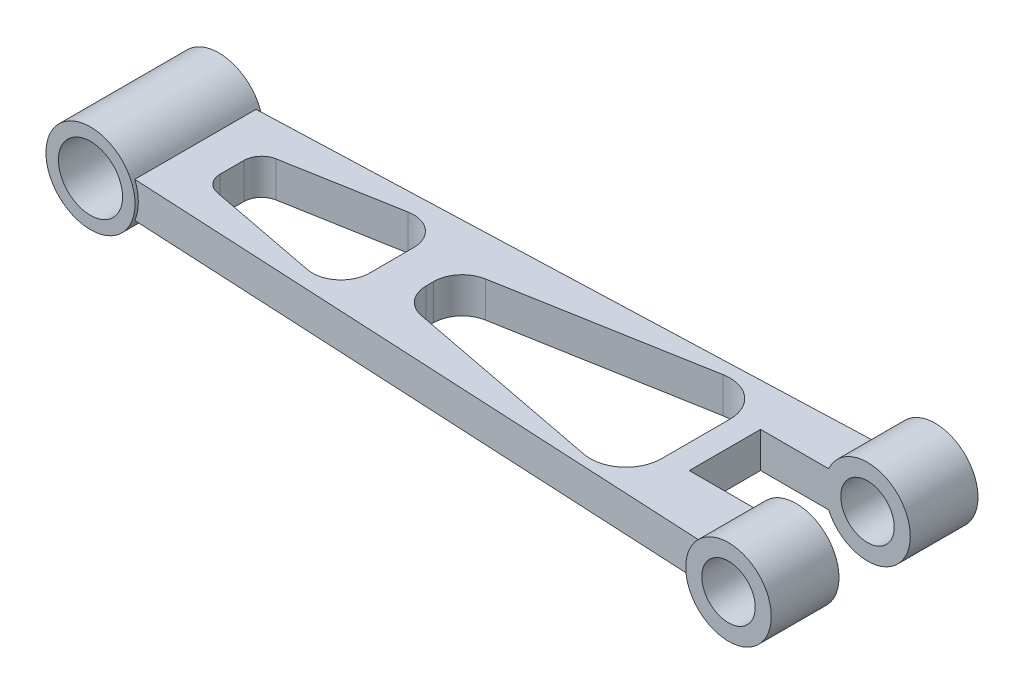
SolidWorks part; units mm, degrees
material "Ti-6Al-4VSolution treated and aged (SS)"
ref_plane "Front Plane" through (0, 0, 0) normal (0, 0, 1) x (1, 0, 0)
ref_plane "Top Plane" through (0, 0, 0) normal (0, 1, 0) x (1, 0, 0)
ref_plane "Right Plane" through (0, 0, 0) normal (1, 0, 0) x (0, 0, -1)
sketch "Sketch1" plane through (0, 0, 0) normal (0, 0, 1) x (1, 0, 0)
  line L0 (-142.6024, 0) -> (128.1696, 0) construction
  line L1 (0, 42.0831) -> (0, -47.0217) construction
  circle A1 centre (-95, 0) radius 9
  dimension "D1" = 18
  dimension "D3" = 95
extrude "Boss-Extrude2" add sketch "Sketch1" along normal mid plane 36
sketch "Sketch2" plane through (0, 0, 0) normal (0, 0, 1) x (1, 0, 0)
  line L0 (-174.7193, 0) -> (396.8583, 0) construction
  circle A1 centre (95, 0) radius 7.5
  dimension "D1" = 15
  dimension "D3" = 95
extrude "Boss-Extrude3" add sketch "Sketch2" along normal mid plane 58 separate body
sketch "Sketch5" plane through (0, 0, 0) normal (0, 1, 0) x (1, 0, 0)
  line L0 (-120.9467, 0) -> (118.8255, 0) construction
  line L1 (-86, -16.9) -> (-86, 16.8979)
  line L2 (-86, -18) -> (-86, 18) construction
  line L3 (-86, 16.8979) -> (87.5, 23.2428)
  line L5 (87.5, 23.2428) -> (87.5, -25.7343)
  line L6 (87.5, -25.7343) -> (-86, -16.9)
  line L7 (87.5, 29) -> (87.5, -29) construction
  point P7 (-55, 18.0315)
  point P12 (-55, -18.4785)
  dimension "D1" = 31
  dimension "D2" = 31
  dimension "D3" = 5.009
  dimension "D4" = 36.51
  dimension "D5" = 48.9771
  dimension "D6" = 23.2428
extrude "Boss-Extrude5" add sketch "Sketch5" along normal mid plane 10 separate body
sketch "Sketch7" plane through (0, 0, 0) normal (0, 0, 1) x (1, 0, 0)
  circle A0 centre (-95, 0) radius 12.5
  dimension "D1" = 25
extrude "Boss-Extrude6" add sketch "Sketch7" along normal mid plane 36
sketch "Sketch8" plane through (0, 0, 0) normal (0, 0, 1) x (1, 0, 0)
  circle A0 centre (95, 0) radius 12
  dimension "D1" = 24
extrude "Boss-Extrude7" add sketch "Sketch8" along normal mid plane 58
sketch "Sketch9" plane through (0, 0, 0) normal (0, 0, 1) x (1, 0, 0)
  circle A0 centre (-95, 0) radius 9
  circle A1 centre (95, 0) radius 7.5
  dimension "D1" = 18
  dimension "D2" = 15
extrude "Cut-Extrude1" cut sketch "Sketch9" against normal mid plane 58
sketch "Sketch10" plane through (0, 5, 0) normal (0, 1, 0) x (1, 0, 0)
  line L0 (-132.4159, 0) -> (132.5611, 0) construction
  line L1 (107, -29) -> (107, 29) construction
  line L2 (65, 10) -> (107, 10)
  line L3 (65, 10) -> (65, -10)
  line L4 (65, -10) -> (107, -10)
  line L5 (107, 10) -> (107, -10)
  dimension "D1" = 20
  dimension "D2" = 42
  dimension "D3" = 10
extrude "Cut-Extrude2" cut sketch "Sketch10" against normal mid plane 58
sketch "Sketch11" plane through (0, 5, 0) normal (0, 1, 0) x (1, 0, 0)
  line L0 (-145.9443, 0) -> (154.4776, 0) construction
  line L1 (-72.8284, 2.8417) -> (-72.8284, -3.7789)
  line L2 (-68.7751, -8.6885) -> (-37.3432, -14.7498)
  line L3 (-27.8284, -6.8945) -> (-27.8284, 5.4913)
  line L4 (-37.2305, 13.3675) -> (-68.7047, 7.7643)
  line L5 (84.0913, 23.1181) -> (-83.5436, 16.9877) construction
  line L6 (-83.5436, -17.0251) -> (84.0913, -25.5608) construction
  line L7 (-16.777, 0.08) -> (-16.777, -2.0525)
  line L8 (-10.2918, -9.9078) -> (46.3295, -20.8266)
  line L9 (58.223, -11.0075) -> (58.223, 8.1961)
  line L10 (46.4703, 18.0413) -> (-10.1792, 7.9562)
  arc A0 (-72.8284, -3.7789) -> (-68.7751, -8.6885) centre (-67.8284, -3.7789) ccw
  arc A1 (-72.8284, 2.8417) -> (-68.7047, 7.7643) centre (-67.8284, 2.8417) cw
  arc A2 (-27.8284, -6.8945) -> (-37.3432, -14.7498) centre (-35.8284, -6.8945) cw
  arc A3 (-27.8284, 5.4913) -> (-37.2305, 13.3675) centre (-35.8284, 5.4913) ccw
  arc A4 (-16.777, -2.0525) -> (-10.2918, -9.9078) centre (-8.777, -2.0525) ccw
  arc A5 (-16.777, 0.08) -> (-10.1792, 7.9562) centre (-8.777, 0.08) cw
  arc A6 (58.223, -11.0075) -> (46.3295, -20.8266) centre (48.223, -11.0075) cw
  arc A7 (58.223, 8.1961) -> (46.4703, 18.0413) centre (48.223, 8.1961) ccw
  dimension "D4" = 5
  dimension "D5" = 8
  dimension "D7" = 8
  dimension "D8" = 10
  dimension "D1" = 45
  dimension "D2" = 8
  dimension "D3" = 8
  dimension "D6" = 75
  dimension "D9" = 8
  dimension "D10" = 8
extrude "Cut-Extrude3" cut sketch "Sketch11" against normal mid plane 58
